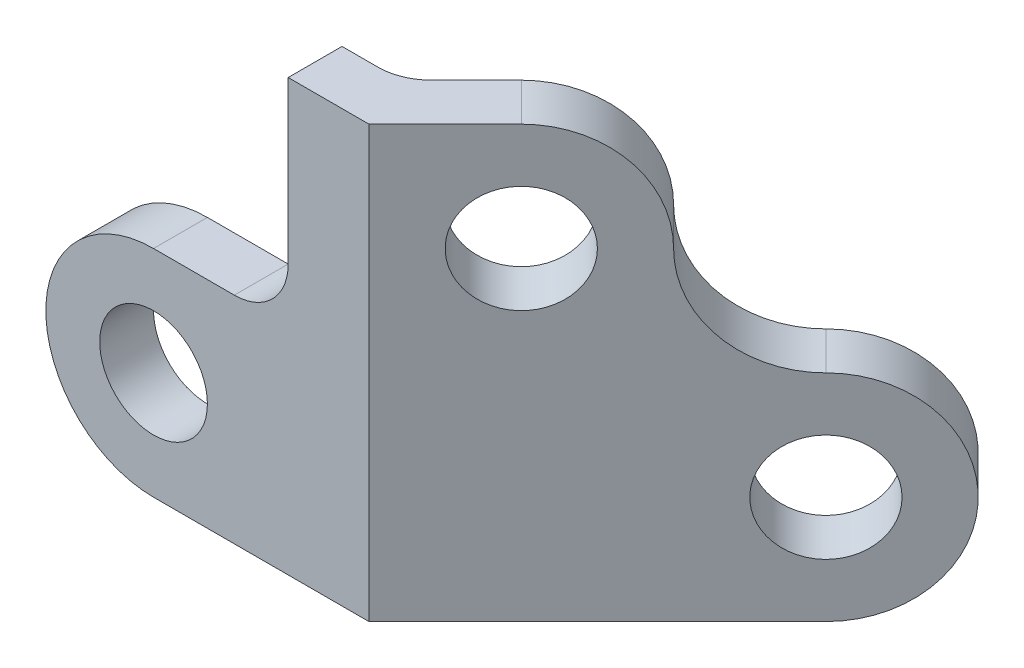
SolidWorks part; units mm, degrees
ref_plane "前基準面" through (0, 0, 0) normal (0, 0, 1) x (1, 0, 0)
ref_plane "上基準面" through (0, 0, 0) normal (0, 1, 0) x (1, 0, 0)
ref_plane "右基準面" through (0, 0, 0) normal (1, 0, 0) x (0, 0, -1)
sketch "草圖1" plane through (0, 0, 0) normal (0, 0, 1) x (1, 0, 0)
  line L0 (0, 80) -> (0, 0)
  line L1 (0, 80) -> (-15, 80)
  line L3 (0, 0) -> (-40, 0)
  line L4 (-40, 40) -> (-25, 40)
  line L5 (-15, 50) -> (-15, 80)
  circle A0 centre (-40, 20) radius 10
  arc A1 (-40, 0) -> (-40, 40) centre (-40, 20) cw
  arc A2 (-15, 50) -> (-25, 40) centre (-25, 50) cw
  dimension "D1" = 10
  dimension "D2" = 20
  dimension "D3" = 20
  dimension "D4" = 80
  dimension "D5" = 15
  dimension "D6" = 40
ref_plane "平面1" through (0, 0, 0) normal (0.7071, 0, 0.7071) x (0, -1, 0)
sketch "草圖2" plane through (0, 0, 0) normal (0.7071, 0, 0.7071) x (0, -1, 0)
  line L4 (0, 60) -> (0, 0)
  line L5 (-80, 0) -> (0, 0)
  line L6 (-80, 20) -> (-80, 0)
  circle A0 centre (-60, 20) radius 10
  circle A1 centre (-20, 60) radius 10
  arc A2 (0, 60) -> (-40, 60) centre (-20, 60) ccw
  arc A3 (-80, 20) -> (-60, 40) centre (-60, 20) cw
  arc A4 (-60, 40) -> (-40, 60) centre (-60, 60) ccw
  dimension "D1" = 20
  dimension "D2" = 20
  dimension "D4" = 20
  dimension "D5" = 20
  dimension "D6" = 20
  dimension "D7" = 20
  dimension "D3" = 60
extrude "填料-伸長1" add sketch "草圖1" against normal blind 10
extrude "填料-伸長2" add sketch "草圖2" against normal blind 10
fillet "圓角1" radius 10 1 edges at (-4.1421, 40, -10)
